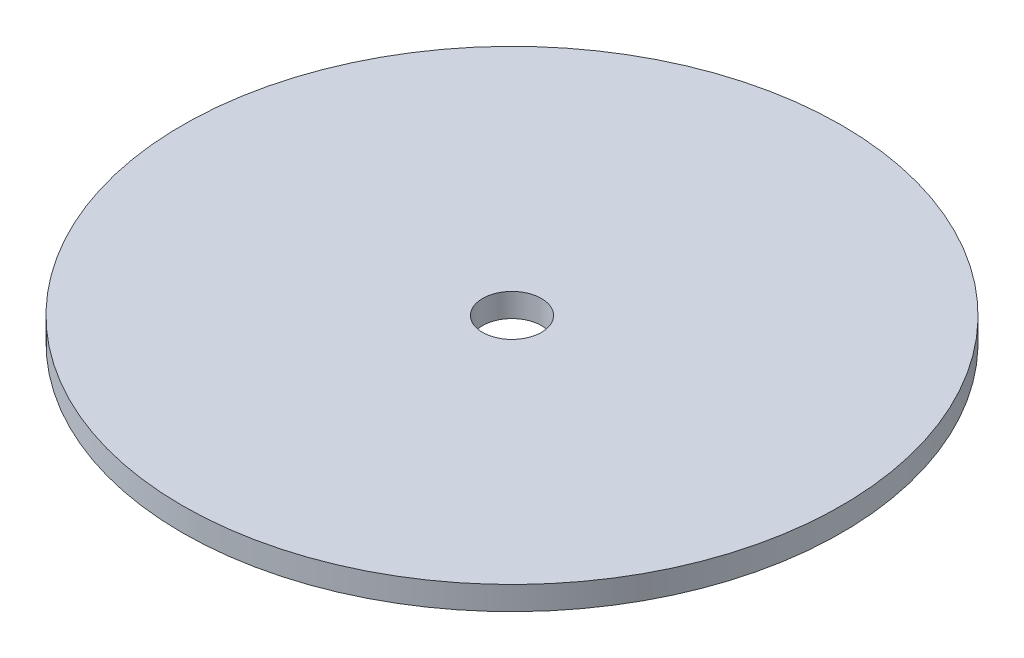
SolidWorks part; units mm, degrees
ref_plane "Front Plane" through (0, 0, 0) normal (0, 0, 1) x (1, 0, 0)
ref_plane "Top Plane" through (0, 0, 0) normal (0, 1, 0) x (1, 0, 0)
ref_plane "Right Plane" through (0, 0, 0) normal (1, 0, 0) x (0, 0, -1)
sketch "Sketch1" plane through (0, 0, 0) normal (0, 0, 1) x (1, 0, 0)
  line L1 (2.5, 0) -> (28, 0)
  line L2 (28, 0) -> (28, 2)
  line L3 (28, 2) -> (2.5, 2)
  line L4 (2.5, 2) -> (2.5, 0)
  line L5 (0, 0) -> (0, 4.4704) construction
revolve "Revolve1" add sketch "Sketch1" angle 360 about L5
sketch "Sketch3" plane through (0, 2, 0) normal (0, 1, 0) x (1, 0, 0)
  line L0 (-28, 0) -> (28, 0)
  circle A0 centre (0, 0) radius 28 construction
